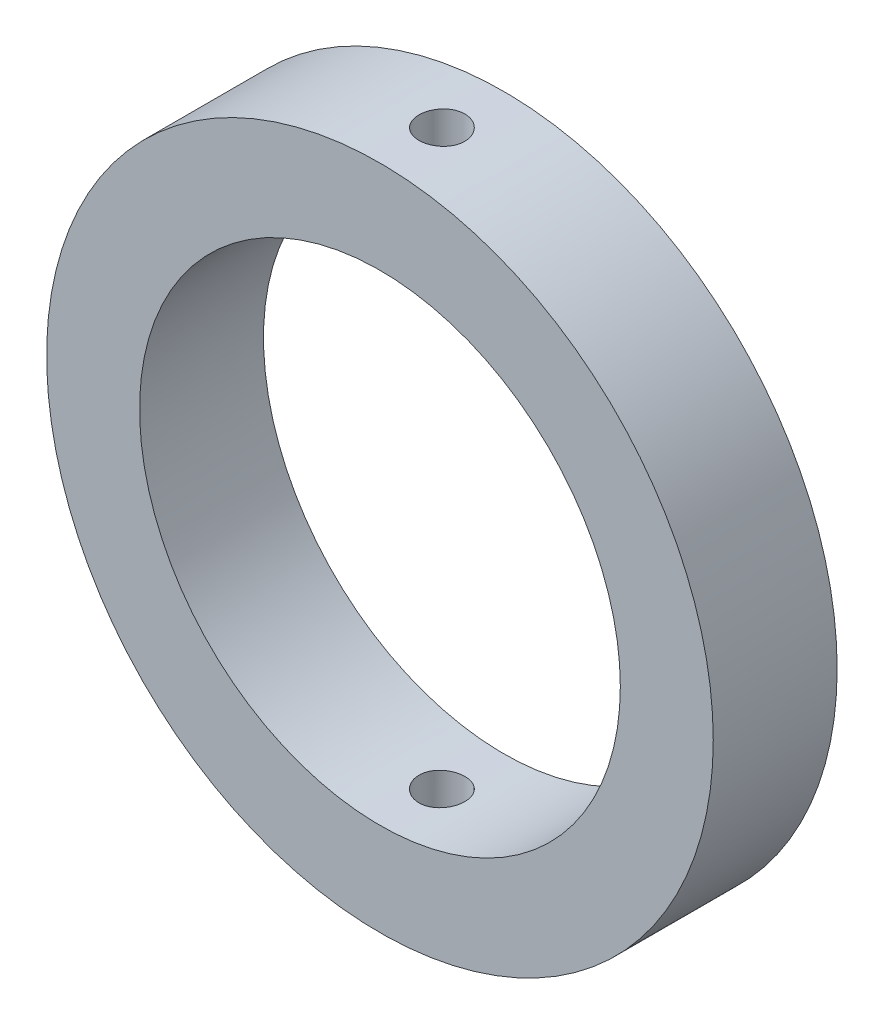
SolidWorks part; units mm, degrees
ref_plane "Front Plane" through (0, 0, 0) normal (0, 0, 1) x (1, 0, 0)
ref_plane "Top Plane" through (0, 0, 0) normal (0, 1, 0) x (1, 0, 0)
ref_plane "Right Plane" through (0, 0, 0) normal (1, 0, 0) x (0, 0, -1)
sketch "Sketch1" plane through (0, 0, 0) normal (0, 0, 1) x (1, 0, 0)
  circle A0 centre (0, 0) radius 68.326
  circle A1 centre (0, 0) radius 49.276
  dimension "D1" = 136.652
  dimension "D2" = 98.552
extrude "Boss-Extrude1" add sketch "Sketch1" along normal blind 25.4
sketch "Sketch2" plane through (0, 0, 0) normal (0, 1, 0) x (1, 0, 0)
  line L0 (0, -1000) -> (0, 49000) construction
  circle A0 centre (0, -12.7) radius 4.699
  dimension "D1" = 9.398
  dimension "D2" = 12.7
extrude "Cut-Extrude1" cut sketch "Sketch2" against normal through all both and the other way through all
